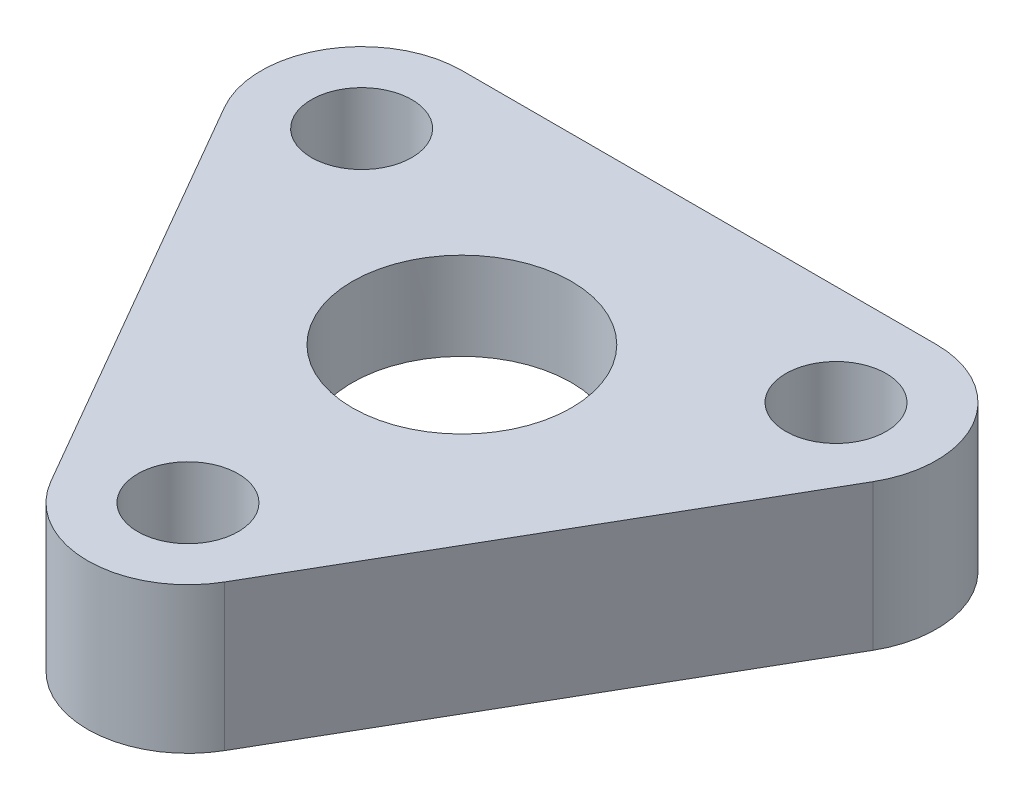
SolidWorks part; units mm, degrees
ref_plane "Front Plane" through (0, 0, 0) normal (0, 0, 1) x (1, 0, 0)
ref_plane "Top Plane" through (0, 0, 0) normal (0, 1, 0) x (1, 0, 0)
ref_plane "Right Plane" through (0, 0, 0) normal (1, 0, 0) x (0, 0, -1)
sketch "Sketch1" plane through (0, 0, 0) normal (0, 1, 0) x (1, 0, 0)
  line L0 (-12.9904, 13) -> (12.9904, 13)
  line L4 (-4.7631, -17.75) -> (-17.7535, 4.75)
  line L5 (0, -15) -> (0, 0) construction
  line L6 (0, 0) -> (-12.9904, 7.5) construction
  line L7 (4.7631, -17.75) -> (17.7535, 4.75)
  circle A0 centre (0, 0) radius 6
  arc A2 (-12.9904, 13) -> (-17.7535, 4.75) centre (-12.9904, 7.5) ccw
  arc A3 (-4.7631, -17.75) -> (4.7631, -17.75) centre (0, -15) ccw
  circle A5 centre (0, 0) radius 11.25 construction
  arc A6 (12.9904, 13) -> (17.7535, 4.75) centre (12.9904, 7.5) cw
  circle A7 centre (-12.9904, 7.5) radius 2.75
  circle A8 centre (12.9904, 7.5) radius 2.75
  circle A9 centre (0, -15) radius 2.75
  point P19 (0, 13)
  point P20 (0, 0)
  dimension "D1" = 12
  dimension "D2" = 22.5
  dimension "D4" = 5.5
  dimension "D5" = 5.5
  dimension "D3" = 13
  dimension "D6" = 120
  dimension "D7" = 3
extrude "Boss-Extrude1" add sketch "Sketch1" along normal blind 8
sketch "Sketch2" plane through (0, 0, 0) normal (0, -1, 0) x (1, 0, 0)
  circle A0 centre (0, 0) radius 11.25 construction
  circle A1 centre (0, 0) radius 11.25
extrude "Cut-Extrude1" cut sketch "Sketch2" against normal blind 3.2
